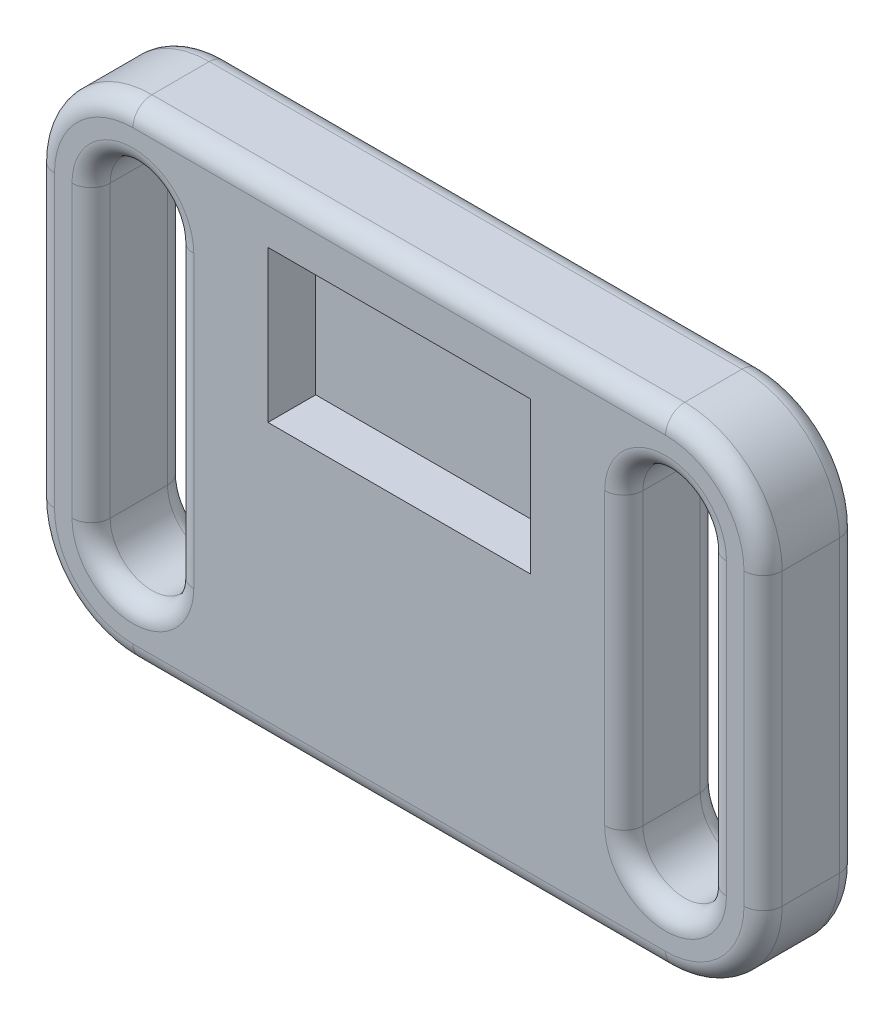
SolidWorks part; units mm, degrees
ref_plane "Front Plane" through (0, 0, 0) normal (0, 0, 1) x (1, 0, 0)
ref_plane "Top Plane" through (0, 0, 0) normal (0, 1, 0) x (1, 0, 0)
ref_plane "Right Plane" through (0, 0, 0) normal (1, 0, 0) x (0, 0, -1)
sketch "Sketch1" plane through (0, 0, 0) normal (0, 0, 1) x (1, 0, 0)
  line L0 (-152.4, -60.7667) -> (-152.4, 60.7667)
  line L1 (-152.4, -101.6) -> (152.4, -101.6) construction
  line L2 (-152.4, -101.6) -> (-152.4, 101.6) construction
  line L3 (-152.4, 101.6) -> (152.4, 101.6) construction
  line L4 (152.4, -101.6) -> (152.4, 101.6) construction
  line L5 (-152.4, -101.6) -> (152.4, 101.6) construction
  line L6 (-152.4, 101.6) -> (152.4, -101.6) construction
  line L7 (-111.5667, 101.6) -> (111.5667, 101.6)
  line L8 (0, 101.6) -> (0, -101.6) construction
  line L9 (152.4, 0) -> (-152.4, 0) construction
  line L10 (-152.4, -101.6) -> (152.4, 101.6) construction
  line L11 (-152.4, -101.6) -> (152.4, -101.6) construction
  line L12 (-111.5667, -101.6) -> (111.5667, -101.6)
  line L13 (152.4, -101.6) -> (-152.4, 101.6) construction
  line L14 (152.4, 101.6) -> (-152.4, -101.6) construction
  line L15 (152.4, -101.6) -> (-152.4, 101.6) construction
  line L16 (152.4, -101.6) -> (152.4, 101.6) construction
  line L17 (152.4, -60.7667) -> (152.4, 60.7667)
  line L18 (-129.0667, 60.7667) -> (-152.4, 60.7667) construction
  line L19 (-129.0667, 60.7667) -> (-94.0667, 60.7667) construction
  line L20 (-129.0667, 60.7667) -> (-129.0667, -60.7667)
  line L21 (-129.0667, -60.7667) -> (-94.0667, -60.7667) construction
  line L22 (-94.0667, 60.7667) -> (-94.0667, -60.7667)
  line L23 (129.0667, 60.7667) -> (129.0667, -60.7667)
  line L24 (94.0667, 60.7667) -> (94.0667, -60.7667)
  arc A0 (-152.4, 60.7667) -> (-111.5667, 101.6) centre (-111.5667, 60.7667) cw
  arc A1 (-152.4, -60.7667) -> (-111.5667, -101.6) centre (-111.5667, -60.7667) ccw
  arc A2 (152.4, -60.7667) -> (111.5667, -101.6) centre (111.5667, -60.7667) cw
  arc A3 (152.4, 60.7667) -> (111.5667, 101.6) centre (111.5667, 60.7667) ccw
  arc A4 (-129.0667, 60.7667) -> (-94.0667, 60.7667) centre (-111.5667, 60.7667) cw
  arc A5 (-129.0667, -60.7667) -> (-94.0667, -60.7667) centre (-111.5667, -60.7667) ccw
  arc A6 (129.0667, -60.7667) -> (94.0667, -60.7667) centre (111.5667, -60.7667) cw
  arc A7 (129.0667, 60.7667) -> (94.0667, 60.7667) centre (111.5667, 60.7667) ccw
  point P0 (0, 0)
  point P17 (0, 0)
  dimension "D1" = 203.2
  dimension "D2" = 304.8
  dimension "D3" = 35
  dimension "D4" = 23.3333
extrude "Steering Wheel Body" add sketch "Sketch1" along normal mid plane 40
fillet "Fillet1" radius 8 32 edges at (111.5667, 78.2667, -20) (129.0667, 0, -20) (111.5667, -78.2667, -20) (94.0667, 0, -20) (-111.5667, -78.2667, -20) (-129.0667, 0, -20) (-111.5667, 78.2667, -20) (-94.0667, 0, -20) (-152.4, 0, -20) (-140.4402, -89.6402, -20) (0, -101.6, -20) (140.4402, -89.6402, -20) (152.4, 0, -20) (140.4402, 89.6402, -20) (0, 101.6, -20) (-140.4402, 89.6402, -20) (129.0667, 0, 20) (111.5667, 78.2667, 20) (94.0667, 0, 20) (111.5667, -78.2667, 20) (0, 101.6, 20) (140.4402, 89.6402, 20) (152.4, 0, 20) (140.4402, -89.6402, 20) (0, -101.6, 20) (-140.4402, -89.6402, 20) (-152.4, 0, 20) (-140.4402, 89.6402, 20) (-129.0667, 0, 20) (-111.5667, -78.2667, 20) (-94.0667, 0, 20) (-111.5667, 78.2667, 20)
sketch "Sketch3" plane through (0, 0, 0) normal (0, 0, 1) x (1, 0, 0)
  line L0 (0, 0) -> (0, 101.6) construction
  line L1 (-54.9926, 15) -> (54.9926, 15)
  line L2 (-54.9926, 15) -> (-54.9926, 78.5)
  line L3 (-54.9926, 78.5) -> (54.9926, 78.5)
  line L4 (54.9926, 15) -> (54.9926, 78.5)
  line L5 (111.5667, 101.6) -> (-111.5667, 101.6) construction
  line L6 (0, 0) -> (152.4, 0) construction
  line L7 (152.4, -60.7667) -> (152.4, 60.7667) construction
  line L8 (-94.0667, -60.7667) -> (-94.0667, 60.7667) construction
  line L9 (-54.9926, 15) -> (54.9926, 78.5) construction
  point P9 (0, 15)
  dimension "D3" = 15
  dimension "D1" = 127
  dimension "D2" = 30
extrude "LCD Cutout" cut sketch "Sketch3" against normal blind 20 from surface at 20 starting at face at (111.5667, 0, 20)
sketch "Sketch5" plane through (0, 0, 0) normal (0, 0, 1) x (1, 0, 0)
  line L0 (0, 0) -> (0, 41.9601) construction
  circle A0 centre (0, 0) radius 41.9601 construction
  point P5 (0, 41.9601)
  dimension "D1" = 83.9201
hole_wizard "M5x0.8 Tapped Hole1" positions "Sketch6" profile "Sketch7" tap size "M5x0.8" standard "ANSI Metric"
sketch "Sketch6" plane through (0, 0, -20) normal (0, 0, -1) x (-1, 0, 0)
  point P0 (0, 41.9601)
sketch "Sketch7" plane through (0, 41.9601, -20) normal (1, 0, 0) x (0, 1, 0)
  line L0 (0, 0) -> (0, 9.6618)
  line L1 (0, 9.6618) -> (2.1, 8.4)
  line L2 (2.1, 8.4) -> (2.1, 0)
  line L5 (2.1, 0) -> (0, 0)
  line L10 (0, 9.6618) -> (-2.1, 8.4) construction
  line L11 (0, -6.35) -> (0, 107.95) construction
  dimension "Tap Drill Dia." = 4.2
  dimension "Tap Drill Depth" = 8.4
  dimension "Drill Angle" = 118
sketch "Sketch8" plane through (0, 0, 0) normal (0, 1, 0) x (1, 0, 0)
  line L0 (0, 52.4568) -> (0, -56.5569) construction
pattern_circular "CirPattern1" count 9 over 360 about axis through (0, 0, 0) along (0, 0, 1) of "M5x0.8 Tapped Hole1"
ref_plane "Plane1" through (0, 0, -30) normal (0, 0, -1) x (-1, 0, 0)
sketch "Sketch9" plane through (0, 0, -30) normal (0, 0, -1) x (-1, 0, 0)
  point P0 (0, 0)
equation "\"Steering Wheel Height\"= 8in"
equation "\"D1@Sketch1\"=\"Steering Wheel Height\""
equation "\"Steering Wheel Width\"= 12in"
equation "\"D2@Sketch1\"=\"Steering Wheel Width\""
equation "\"Steering Wheel Thickness\"= 35mm"
equation "\"Hand Cutout Width\"= 35mm"
equation "\"D3@Sketch1\"=\"Hand Cutout Width\""
equation "\"D4@Sketch1\"=\"Hand Cutout Width\"*(2/3)"
equation "\"LCD Width\"= \"LCD Size\" * cos ( 30deg )"
equation "\"LCD Height\"= \"LCD Size\" * sin ( 30deg )"
equation "\"LCD Thickness\"= 2cm'Exact thickness is unknown at this time for the LCD specced out"
equation "\"D1@LCD Cutout\" = \"LCD Thickness\""
equation "\"LCD Size\"= 5in"
equation "\"D1@Sketch3\"=\"LCD Size\""
equation "\"Quick Release Diameter\"=83.9201"
equation "\"D1@Sketch5\"=\"Quick Release Diameter\""
equation "\"Number of Holes on Quick Release\"=9"
